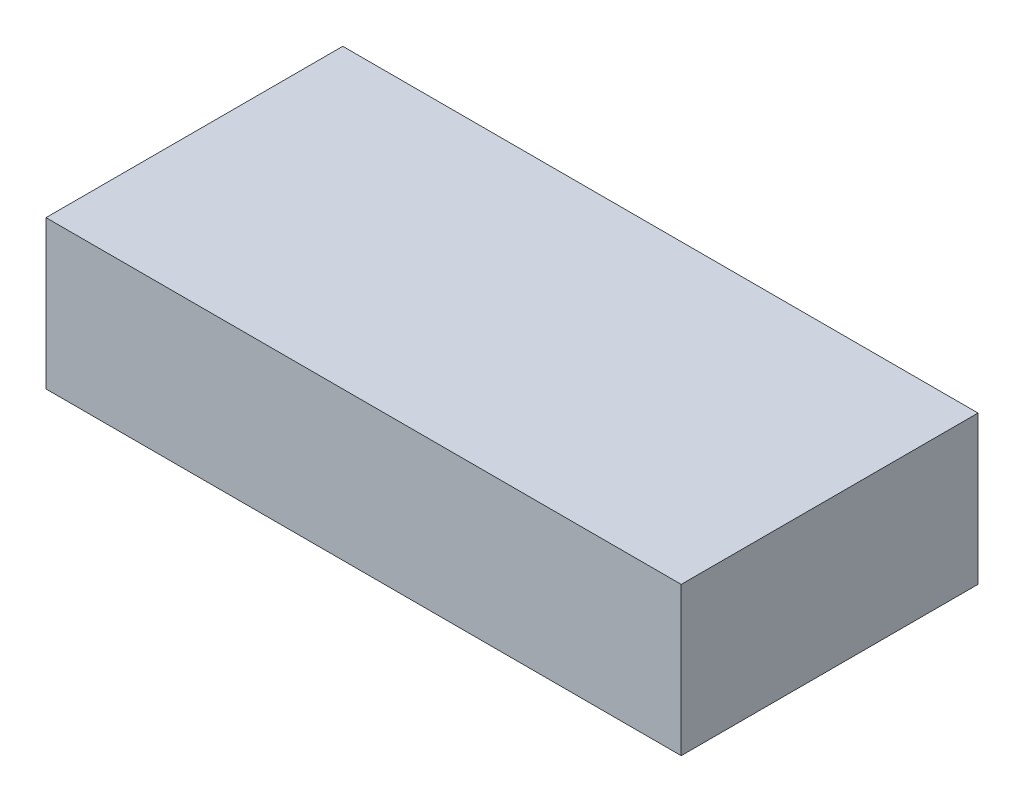
SolidWorks part; units mm, degrees
ref_plane "Alzado" through (0, 0, 0) normal (0, 0, 1) x (1, 0, 0)
ref_plane "Planta" through (0, 0, 0) normal (0, 1, 0) x (1, 0, 0)
ref_plane "Vista lateral" through (0, 0, 0) normal (1, 0, 0) x (0, 0, -1)
sketch "Croquis1" plane through (0, 0, 0) normal (0, 1, 0) x (1, 0, 0)
  line L1 (-244, 114) -> (244, 114)
  line L2 (-244, 114) -> (-244, -114)
  line L3 (-244, -114) -> (244, -114)
  line L4 (244, 114) -> (244, -114)
  line L5 (-244, 114) -> (244, -114) construction
  line L6 (-244, -114) -> (244, 114) construction
  point P0 (0, 0)
  dimension "D1" = 488
  dimension "D2" = 228
extrude "Saliente-Extruir1" add sketch "Croquis1" along normal blind 114
